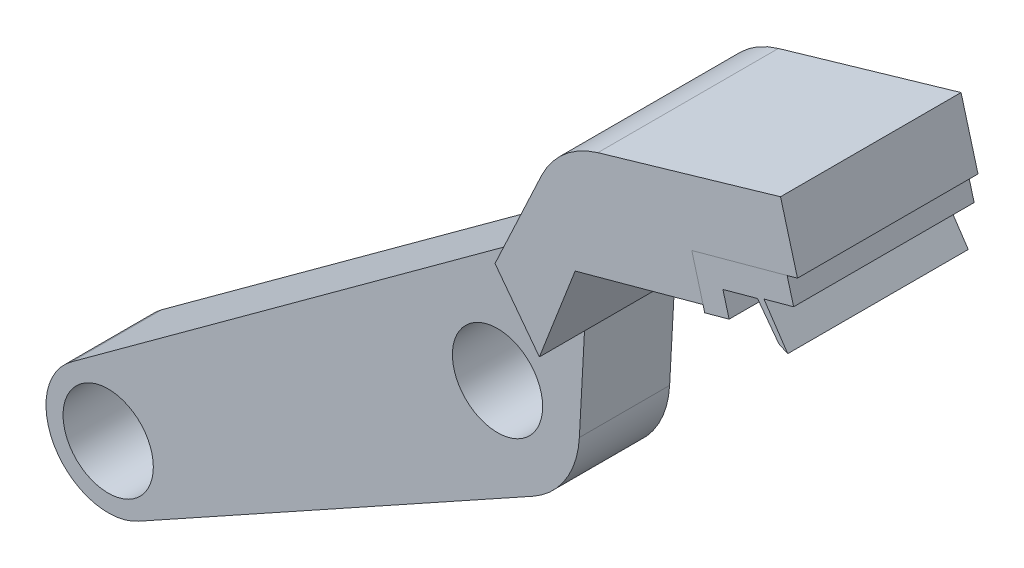
SolidWorks part; units mm, degrees
ref_plane "前视基准面" through (0, 0, 0) normal (0, 0, 1) x (1, 0, 0)
ref_plane "上视基准面" through (0, 0, 0) normal (0, 1, 0) x (1, 0, 0)
ref_plane "右视基准面" through (0, 0, 0) normal (1, 0, 0) x (0, 0, -1)
sketch "草图1" plane through (0, 0, 0) normal (0, 0, 1) x (1, 0, 0)
  line L0 (10.2077, 20.0985) -> (-47.1937, -21.7968)
  line L1 (-39.787, -33.3899) -> (3.9339, -9.1312)
  line L2 (9.0674, -0.9285) -> (10.2077, 20.0985)
  circle A0 centre (0, 0) radius 5
  arc A1 (-47.1937, -21.7968) -> (-39.787, -33.3899) centre (-43.1307, -27.3636) ccw
  circle A2 centre (-43.1307, -27.3636) radius 5
  arc A3 (3.9339, -9.1312) -> (9.0674, -0.9285) centre (-0.9179, -0.387) ccw
  dimension "D1" = 10
  dimension "D2" = 50
extrude "凸台-拉伸1" add sketch "草图1" along normal blind 10
ref_plane "基准面1" through (0, 0, 5) normal (0, 0, 1) x (1, 0, 0)
sketch "草图2" plane through (0, 0, 5) normal (0, 0, 1) x (1, 0, 0)
  line L0 (9.6376, 9.585) -> (13.6022, 19.8126)
  line L1 (9.0674, -0.9285) -> (10.2077, 20.0985) construction
  line L2 (13.6022, 19.8126) -> (27.7686, 23.6802)
  line L3 (27.7686, 23.6802) -> (26.5228, 28.2433)
  line L4 (26.5228, 28.2433) -> (38.2304, 31.4395)
  line L5 (38.2304, 31.4395) -> (36.3536, 38.3141)
  line L6 (36.3536, 38.3141) -> (16.1138, 32.4235)
  line L7 (9.8498, 27.0579) -> (4.7235, 16.0958)
  line L8 (4.7235, 16.0958) -> (9.6376, 9.585)
  line L9 (10.2077, 20.0985) -> (-47.1937, -21.7968) construction
  arc A0 (16.1138, 32.4235) -> (9.8498, 27.0579) centre (18.9083, 22.8219) ccw
  dimension "D1" = 10
extrude "凸台-拉伸2" add sketch "草图2" along normal mid plane 20
sketch "草图3" plane through (0, 0, 5) normal (0, 0, 1) x (1, 0, 0)
  line L0 (27.9595, 22.981) -> (26.5228, 28.2433)
  line L1 (26.5228, 28.2433) -> (37.0836, 31.1265)
  line L2 (26.5228, 28.2433) -> (38.2304, 31.4395) construction
  line L3 (37.0836, 31.1265) -> (37.8052, 28.4832)
  line L4 (37.8052, 28.4832) -> (34.5167, 27.5854)
  line L5 (34.5167, 27.5854) -> (37.1502, 23.651)
  line L6 (36.1644, 24.1146) -> (37.1502, 23.651)
  line L7 (36.1644, 24.1146) -> (33.8059, 27.2793)
  line L8 (33.8059, 27.2793) -> (29.972, 26.2326)
  line L9 (29.972, 26.2326) -> (30.6586, 23.7179)
  line L10 (30.6586, 23.7179) -> (27.9595, 22.981)
extrude "凸台-拉伸3" add sketch "草图3" along normal mid plane 20 separate body
